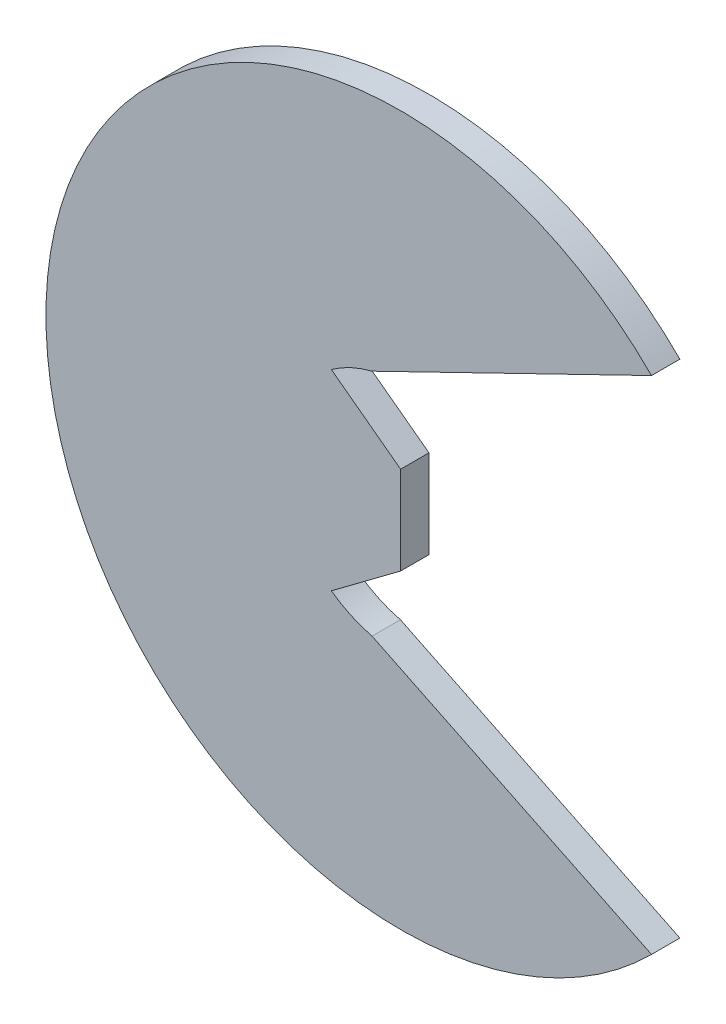
SolidWorks part; units mm, degrees
material "Stainless Steel (ferritic)"
ref_plane "Front Plane" through (0, 0, 0) normal (0, 0, 1) x (1, 0, 0)
ref_plane "Top Plane" through (0, 0, 0) normal (0, 1, 0) x (1, 0, 0)
ref_plane "Right Plane" through (0, 0, 0) normal (1, 0, 0) x (0, 0, -1)
sketch "Sketch1" plane through (0, 0, 0) normal (0, 0, 1) x (1, 0, 0)
  circle A0 centre (0, 0) radius 3.75
  dimension "D1" = 7.5
extrude "Boss-Extrude1" add sketch "Sketch1" along normal blind 0.3
sketch "Sketch2" plane through (0, 0, 0.3) normal (0, 0, 1) x (1, 0, 0)
  line L0 (0, 0.4664) -> (-0.7321, 1.0132)
  line L3 (-0.3018, 1.213) -> (2.653, 2.6503)
  line L4 (-0.3018, -1.213) -> (2.653, -2.6503)
  line L7 (0, -0.4664) -> (-0.7321, -1.0132)
  line L8 (0, -0.4664) -> (0, 0.4664)
  circle A0 centre (0, 0) radius 3.75 construction
  arc A1 (-0.7321, -1.0132) -> (-0.3018, -1.213) centre (0, 0) ccw
  arc A2 (2.653, -2.6503) -> (2.653, 2.6503) centre (0, 0) ccw
  arc A3 (-0.3018, 1.213) -> (-0.7321, 1.0132) centre (0, 0) ccw
extrude "Cut-Extrude2" cut sketch "Sketch2" against normal through all
